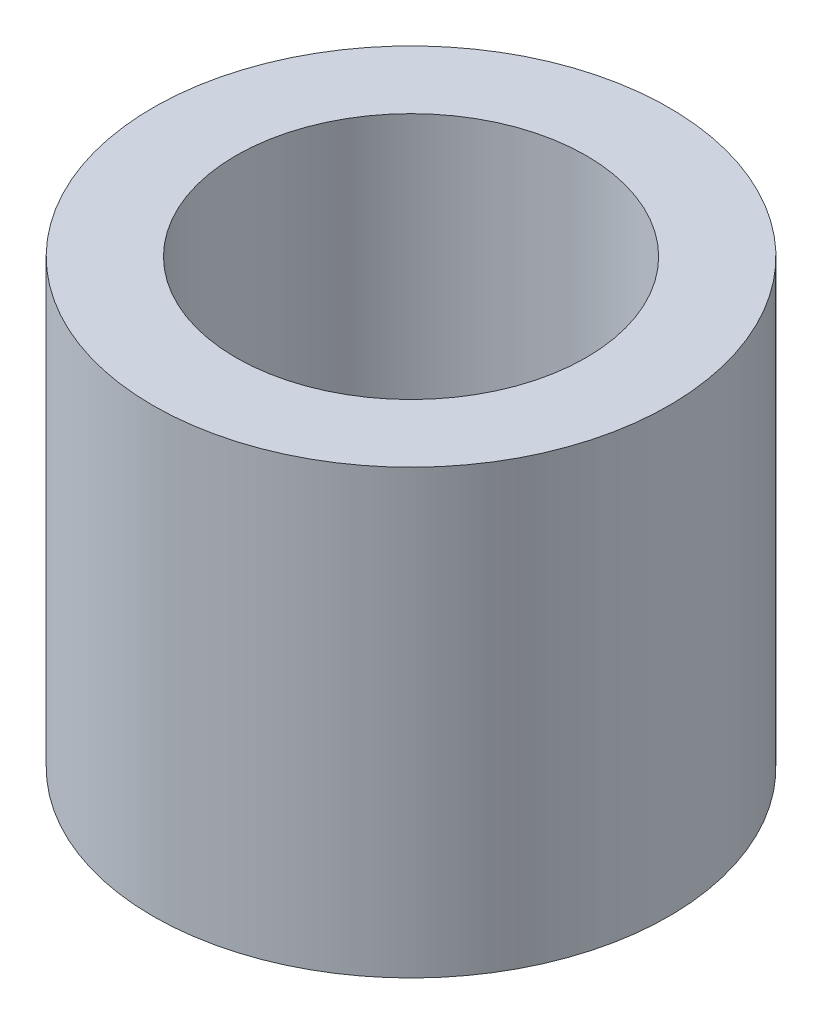
SolidWorks part; units mm, degrees
material "HTPB"
ref_plane "Front Plane" through (0, 0, 0) normal (0, 0, 1) x (1, 0, 0)
ref_plane "Top Plane" through (0, 0, 0) normal (0, 1, 0) x (1, 0, 0)
ref_plane "Right Plane" through (0, 0, 0) normal (1, 0, 0) x (0, 0, -1)
sketch "Sketch1" plane through (0, 0, 0) normal (0, 1, 0) x (1, 0, 0)
  circle A0 centre (0, 0) radius 30.1625
  circle A1 centre (0, 0) radius 44.45
  dimension "D1" = 60.325
  dimension "D2" = 88.9
extrude "Boss-Extrude1" add sketch "Sketch1" along normal blind 76.2
